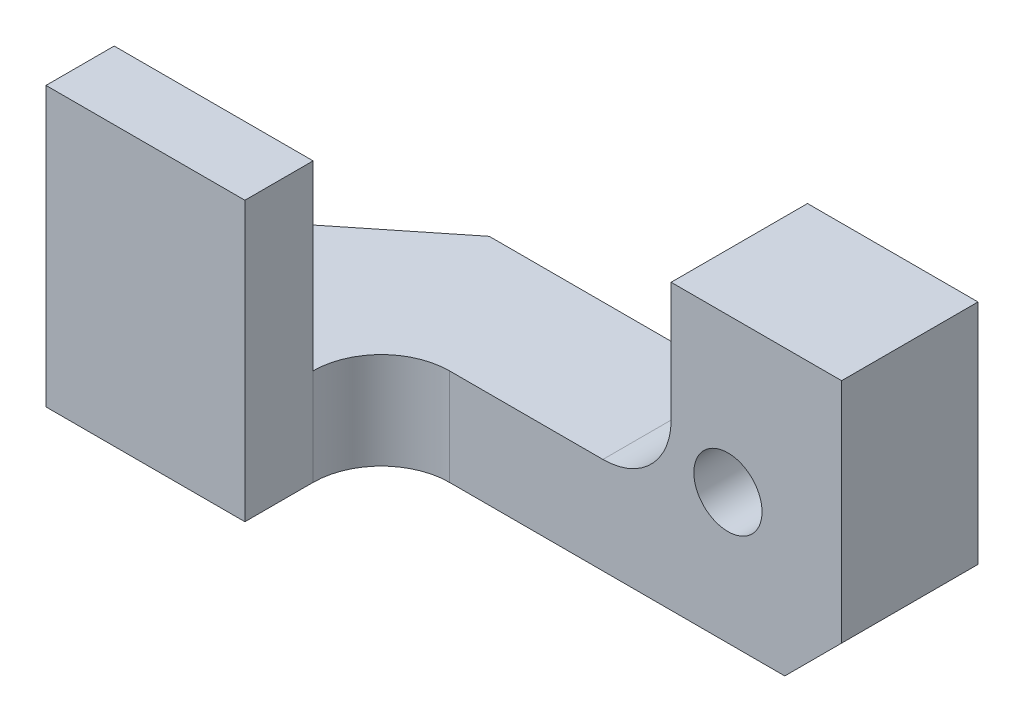
SolidWorks part; units mm, degrees
ref_plane "Front Plane" through (0, 0, 0) normal (0, 0, 1) x (1, 0, 0)
ref_plane "Top Plane" through (0, 0, 0) normal (0, 1, 0) x (1, 0, 0)
ref_plane "Right Plane" through (0, 0, 0) normal (1, 0, 0) x (0, 0, -1)
sketch "Sketch1" plane through (0, 0, 0) normal (0, 1, 0) x (1, 0, 0)
  line L1 (7.366, -3.048) -> (-7.366, -3.048)
  line L2 (7.366, -3.048) -> (7.366, 3.048)
  line L3 (7.366, 3.048) -> (-7.366, 3.048)
  line L4 (-7.366, -3.048) -> (-7.366, 3.048)
  line L5 (7.366, -3.048) -> (-7.366, 3.048) construction
  line L6 (7.366, 3.048) -> (-7.366, -3.048) construction
  point P0 (0, 0)
  dimension "D1" = 14.732
  dimension "D2" = 6.096
extrude "Boss-Extrude1" add sketch "Sketch1" along normal blind 6.35
sketch "Sketch4" plane through (0, 6.35, 0) normal (0, 1, 0) x (1, 0, 0)
  line L0 (-2.921, 0) -> (-1.397, 0)
  line L1 (7.366, -3.048) -> (-2.921, -3.048)
  line L2 (7.366, -3.048) -> (7.366, 0)
  line L3 (7.366, 0) -> (-2.921, 0)
  line L4 (-2.921, -3.048) -> (-2.921, 0)
  line L5 (-1.397, 0) -> (-1.397, -3.048)
  line L6 (-2.921, -1.524) -> (-2.921, 0)
  circle A0 centre (-1.397, -1.524) radius 1.524
  line M2 (-7.366, -3.048) -> (7.366, -3.048)
  line M3 (7.366, -3.048) -> (7.366, 3.048)
  dimension "D1" = 3.048
  dimension "D2" = 10.287
  dimension "D3" = 1.524
extrude "Cut-Extrude2" cut sketch "Sketch4" against normal through all contours A0 L1 L3 M3 | L5 A0 | L5 A0 | A0 L4 M2
sketch "Sketch3" plane through (0, 6.35, 0) normal (0, 1, 0) x (1, 0, 0)
  line L0 (-7.366, -3.048) -> (-2.921, -3.048) construction
  line L1 (-7.366, 3.048) -> (3.556, 3.048)
  line L2 (-7.366, 3.048) -> (-7.366, -3.048)
  line L3 (-7.366, -3.048) -> (3.556, -3.048)
  line L4 (3.556, 3.048) -> (3.556, -3.048)
  dimension "D1" = 10.922
extrude "Cut-Extrude1" cut sketch "Sketch3" against normal blind 2.667
sketch "Sketch8" plane through (0, 3.683, 0) normal (0, 1, 0) x (1, 0, 0)
  line L1 (-7.366, 3.048) -> (-7.366, -3.048) construction
  line L3 (3.556, 3.048) -> (-7.366, 3.048) construction
  line L4 (-3.556, 3.048) -> (-7.366, 0)
  line L5 (-7.366, 3.048) -> (-3.556, 3.048)
  line M4 (3.556, 3.048) -> (-7.366, 3.048)
  line M5 (-7.366, 3.048) -> (-7.366, -3.048)
  dimension "D1" = 3.81
extrude "Cut-Extrude3" cut sketch "Sketch8" against normal through all contours L4 M4 M5
sketch "Sketch9" plane through (0, 3.683, 0) normal (0, 1, 0) x (1, 0, 0)
  line L0 (-7.366, 0) -> (-7.366, -3.048) construction
  line L1 (-2.921, -3.048) -> (-7.366, -3.048)
  line L2 (-2.921, -3.048) -> (-2.921, -1.524)
  line L3 (-2.921, -1.524) -> (-7.366, -1.524)
  line L4 (-7.366, -3.048) -> (-7.366, -1.524)
  dimension "D1" = 1.524
extrude "Boss-Extrude2" add sketch "Sketch9" along normal blind 2.54
sketch "Sketch10" plane through (0, 0, -3.048) normal (0, 0, -1) x (-1, 0, 0)
  line L0 (-7.366, 1.27) -> (-6.096, 0)
  line L1 (-7.366, 6.35) -> (-7.366, 0) construction
  line L2 (-7.366, 0) -> (3.556, 0) construction
  line L3 (-6.096, 0) -> (-7.366, 0)
  line L4 (-7.366, 0) -> (-7.366, 1.27)
  dimension "D1" = 1.27
  dimension "D2" = 1.27
extrude "Cut-Extrude4" cut sketch "Sketch10" against normal through all
sketch "Sketch12" plane through (0, 0, -3.048) normal (0, 0, -1) x (-1, 0, 0)
  line L0 (-2.032, 2.159) -> (-2.032, 3.683)
  line L2 (3.556, 3.683) -> (-3.556, 3.683)
  line L3 (3.556, 3.683) -> (3.556, 2.159)
  line L4 (3.556, 2.159) -> (-3.556, 2.159)
  line L5 (-3.556, 3.683) -> (-3.556, 2.159)
  line L6 (-2.032, 2.159) -> (-3.556, 2.159)
  line L7 (3.556, 3.683) -> (2.921, 3.683)
  line L8 (3.556, 3.683) -> (2.921, 3.683)
  line L9 (3.556, 3.683) -> (3.556, 2.159)
  line L10 (3.556, 2.159) -> (2.921, 2.159)
  line L11 (2.921, 3.683) -> (2.921, 2.159)
  circle A0 centre (-2.032, 3.683) radius 1.524
  line M4 (3.556, 0) -> (3.556, 3.683)
  line M5 (3.556, 3.683) -> (-3.556, 3.683)
  dimension "D1" = 1.524
  dimension "D2" = 1.524
  dimension "D3" = 0.635
extrude "Cut-Extrude5" cut sketch "Sketch12" against normal blind 4.191 contours A0 L4 M4 M5 | L0 A0 L2 | A0 L0 M5
sketch "Sketch13" plane through (0, 0, -3.048) normal (0, 0, -1) x (-1, 0, 0)
  line L1 (2.921, 2.159) -> (7.366, 2.159)
  line L2 (2.921, 2.159) -> (2.921, 3.683)
  line L3 (2.921, 3.683) -> (7.366, 3.683)
  line L4 (7.366, 2.159) -> (7.366, 3.683)
  dimension "D1" = 4.445
sketch "Sketch14" plane through (0, 0, 1.143) normal (0, 0, -1) x (-1, 0, 0)
  line L0 (2.8726, 3.683) -> (2.921, 3.683)
sketch "Sketch15" plane through (0, 0, 1.143) normal (0, 0, -1) x (-1, 0, 0)
  line L1 (2.921, 2.159) -> (2.8726, 2.159)
  line L2 (2.921, 2.159) -> (2.921, 3.683)
  line L3 (2.921, 3.683) -> (2.8726, 3.683)
  line L4 (2.8726, 2.159) -> (2.8726, 3.683)
extrude "Cut-Extrude10" cut sketch "Sketch15" against normal through all
extrude "Cut-Extrude11" cut sketch "Sketch13" against normal blind 4.572
sketch "Sketch16" plane through (0, 0, -3.048) normal (0, 0, -1) x (-1, 0, 0)
  line L0 (-3.556, 3.683) -> (-3.556, 6.35) construction
  line L1 (3.556, 2.159) -> (-2.032, 2.159) construction
  circle A0 centre (-4.826, 2.921) radius 0.762
  dimension "D1" = 1.27
  dimension "D2" = 0.762
extrude "Cut-Extrude12" cut sketch "Sketch16" against normal blind 4.572
